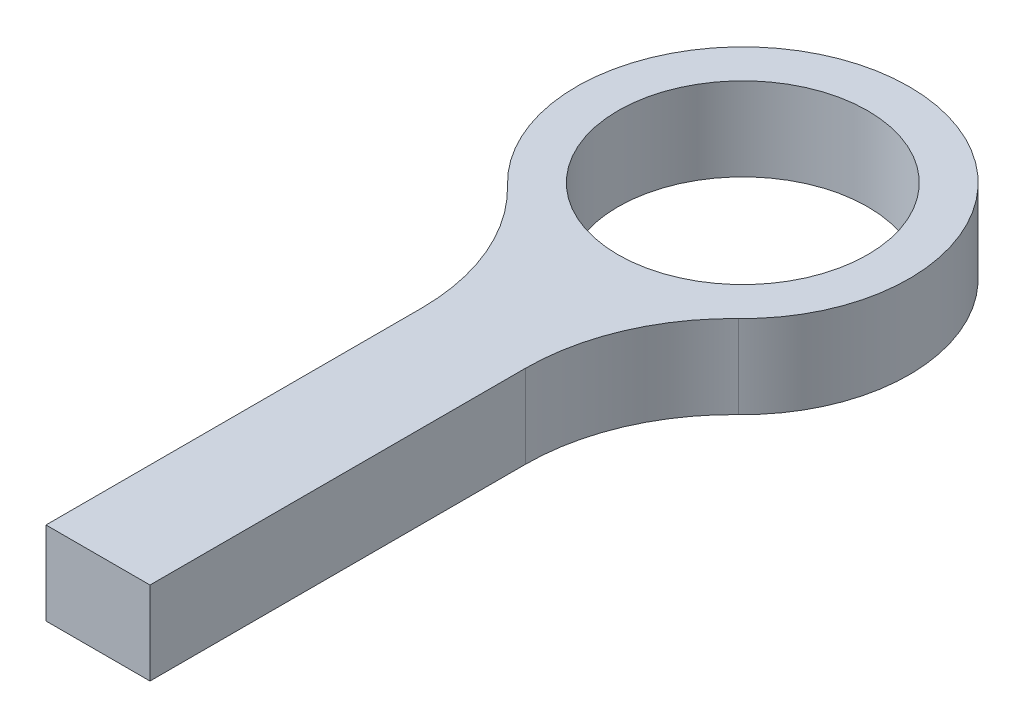
SolidWorks part; units mm, degrees
material "Nylon 101"
ref_plane "Front Plane" through (0, 0, 0) normal (0, 0, 1) x (1, 0, 0)
ref_plane "Top Plane" through (0, 0, 0) normal (0, 1, 0) x (1, 0, 0)
ref_plane "Right Plane" through (0, 0, 0) normal (1, 0, 0) x (0, 0, -1)
sketch "Sketch1" plane through (0, 0, 0) normal (0, 1, 0) x (1, 0, 0)
  line L2 (-2.5, -12.9518) -> (-2.5, -31)
  line L3 (-2.5, -31) -> (2.5, -31)
  line L4 (2.5, -12.9518) -> (2.5, -31)
  circle A0 centre (0, 0) radius 6
  arc A1 (5.5556, -5.7564) -> (-5.5556, -5.7564) centre (0, 0) ccw
  arc A4 (5.5556, -5.7564) -> (2.5, -12.9518) centre (12.5, -12.9518) ccw
  arc A5 (-5.5556, -5.7564) -> (-2.5, -12.9518) centre (-12.5, -12.9518) cw
  dimension "D1" = 2
  dimension "D2" = 12
  dimension "D4" = 31
  dimension "D5" = 10
  dimension "D3" = 5
extrude "Boss-Extrude1" add sketch "Sketch1" along normal blind 4
